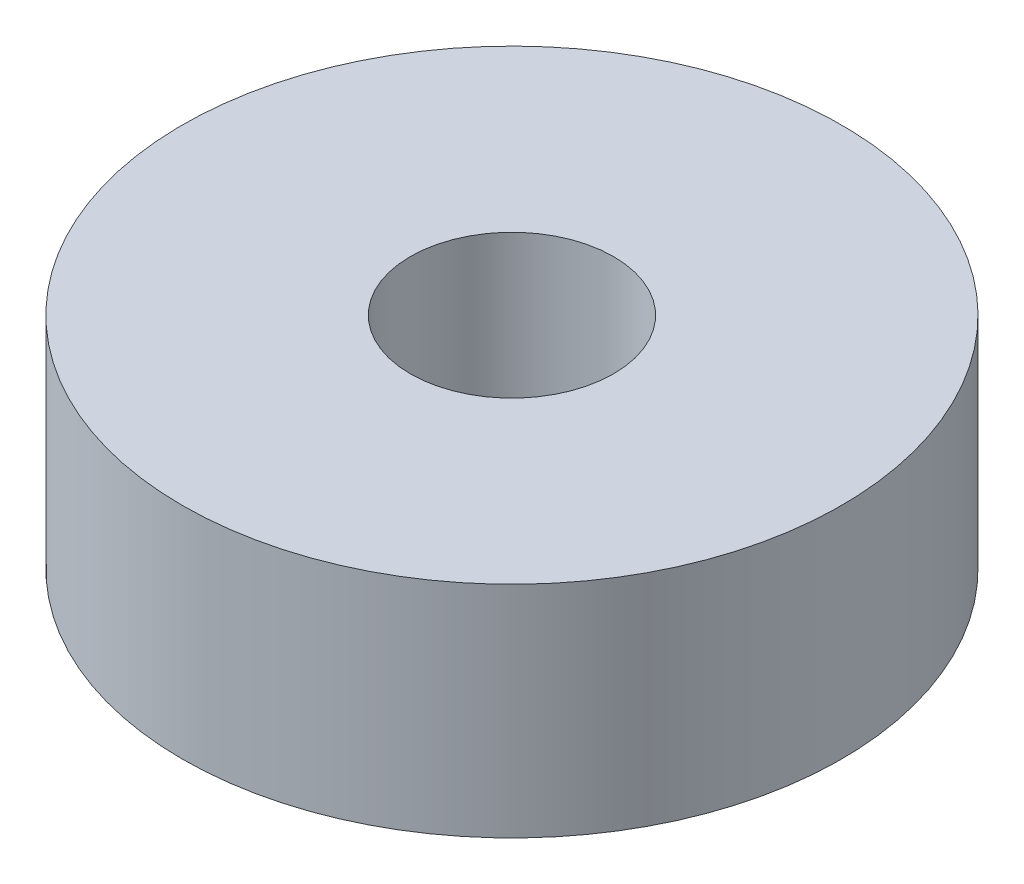
SolidWorks part; units mm, degrees
ref_plane "Front Plane" through (0, 0, 0) normal (0, 0, 1) x (1, 0, 0)
ref_plane "Top Plane" through (0, 0, 0) normal (0, 1, 0) x (1, 0, 0)
ref_plane "Right Plane" through (0, 0, 0) normal (1, 0, 0) x (0, 0, -1)
sketch "Sketch1" plane through (0, 0, 0) normal (0, 1, 0) x (1, 0, 0)
  circle A0 centre (0, 0) radius 1.85
  circle A1 centre (0, 0) radius 6
  dimension "D1" = 3.7
  dimension "D2" = 12
extrude "Boss-Extrude1" add sketch "Sketch1" along normal mid plane 4
